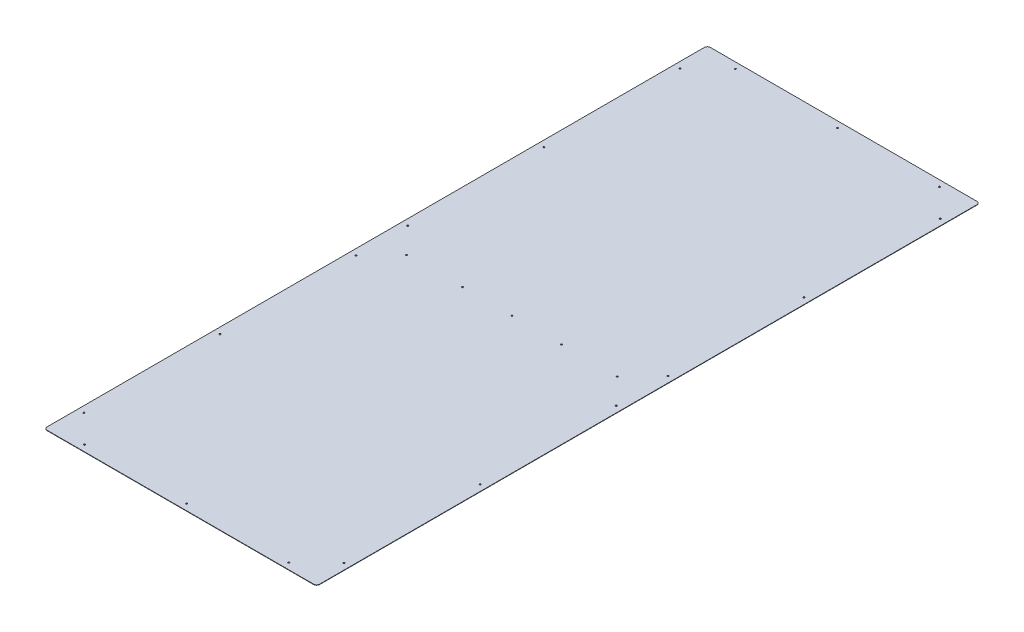
SolidWorks part; units mm, degrees
ref_plane "Front Plane" through (0, 0, 0) normal (0, 0, 1) x (1, 0, 0)
ref_plane "Top Plane" through (0, 0, 0) normal (0, 1, 0) x (1, 0, 0)
ref_plane "Right Plane" through (0, 0, 0) normal (1, 0, 0) x (0, 0, -1)
sketch "Sketch1" plane through (0, 0, 0) normal (0, 1, 0) x (1, 0, 0)
  line L1 (-279.5524, -680.3644) -> (279.5524, -680.3644)
  line L2 (-279.5524, -680.3644) -> (-279.5524, 680.3644)
  line L3 (-279.5524, 680.3644) -> (279.5524, 680.3644)
  line L4 (279.5524, -680.3644) -> (279.5524, 680.3644)
  line L5 (-279.5524, -680.3644) -> (279.5524, 680.3644) construction
  line L6 (-279.5524, 680.3644) -> (279.5524, -680.3644) construction
  point P0 (0, 0)
  dimension "D1" = 1360.7288
  dimension "D2" = 559.1048
extrude "Boss-Extrude1" add sketch "Sketch1" along normal blind 0.7937
fillet "Fillet1" radius 6.35 4 edges at (-279.5524, 0.3969, -680.3644) (279.5524, 0.3969, -680.3644) (-279.5524, 0.3969, 680.3644) (279.5524, 0.3969, 680.3644)
hole_wizard "1/8 (0.125) Diameter Hole1" positions "Sketch2" profile "Sketch3" hole size "1/8" standard "ANSI Inch" end condition through all
sketch "Sketch2" plane through (0, 0, 0) normal (0, -1, 0) x (-1, 0, 0)
  point P0 (-266.8524, -611.632)
  point P3 (-209.55, -667.6644)
  point P6 (-266.8524, -332.232)
  point P9 (0, -667.6644)
  point P12 (209.55, -667.6644)
  point P15 (266.8524, -611.632)
  point P18 (266.8524, -332.232)
  point P27 (266.8524, -52.832)
  point P30 (266.8524, 52.9082)
  point P33 (-266.8524, -52.832)
  point P35 (-266.8524, 52.9082)
  point P41 (-266.8524, 332.3082)
  point P44 (-266.8524, 611.7082)
  point P47 (-209.55, 667.7406)
  point P50 (0, 667.7406)
  point P53 (266.8524, 332.3082)
  point P56 (266.8524, 611.632)
  point P58 (209.55, 667.7406)
  point P65 (-216.0524, 0)
  point P68 (-101.7524, 0)
  point P71 (0, 0)
  point P74 (101.7524, 0)
  point P77 (216.0524, 0)
sketch "Sketch3" plane through (266.8524, 0, 611.632) normal (1, 0, 0) x (0, 0, -1)
  line L0 (0, 0) -> (0, 0.7937)
  line L1 (0, 0.7937) -> (1.5875, 0.7937)
  line L2 (1.5875, 0.7937) -> (1.5875, 0)
  line L5 (1.5875, 0) -> (0, 0)
  line L11 (0, -6.35) -> (0, 107.95) construction
  dimension "Thru Hole Dia." = 3.175
  dimension "Thru Hole Depth" = 0.7937
